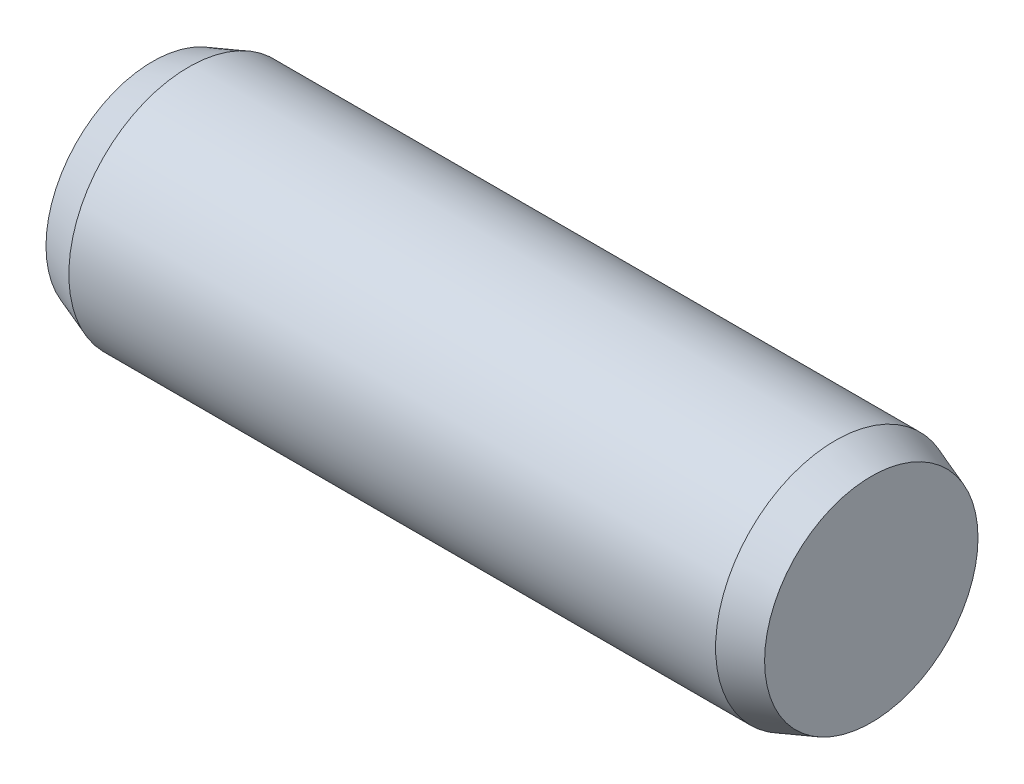
SolidWorks part; units mm, degrees
ref_plane "Front" through (0, 0, 0) normal (0, 0, 1) x (1, 0, 0)
ref_plane "Top" through (0, 0, 0) normal (0, 1, 0) x (1, 0, 0)
ref_plane "Right" through (0, 0, 0) normal (1, 0, 0) x (0, 0, -1)
sketch "Sketch1" plane through (0, 0, 0) normal (0, 0, 1) x (1, 0, 0)
  line L0 (-3, 0.8909) -> (-3, 0)
  line L1 (-3, 0) -> (3, 0)
  line L2 (3, 0) -> (3, 0.8909)
  line L3 (3, 0.8909) -> (2.7, 1.0001)
  line L4 (2.7, 1.0001) -> (-2.7, 1.0001)
  line L5 (-2.7, 1.0001) -> (-3, 0.8909)
  line L6 (-3, 0) -> (3, 0) construction
revolve "Revolve1" add sketch "Sketch1" angle 360 about L6
